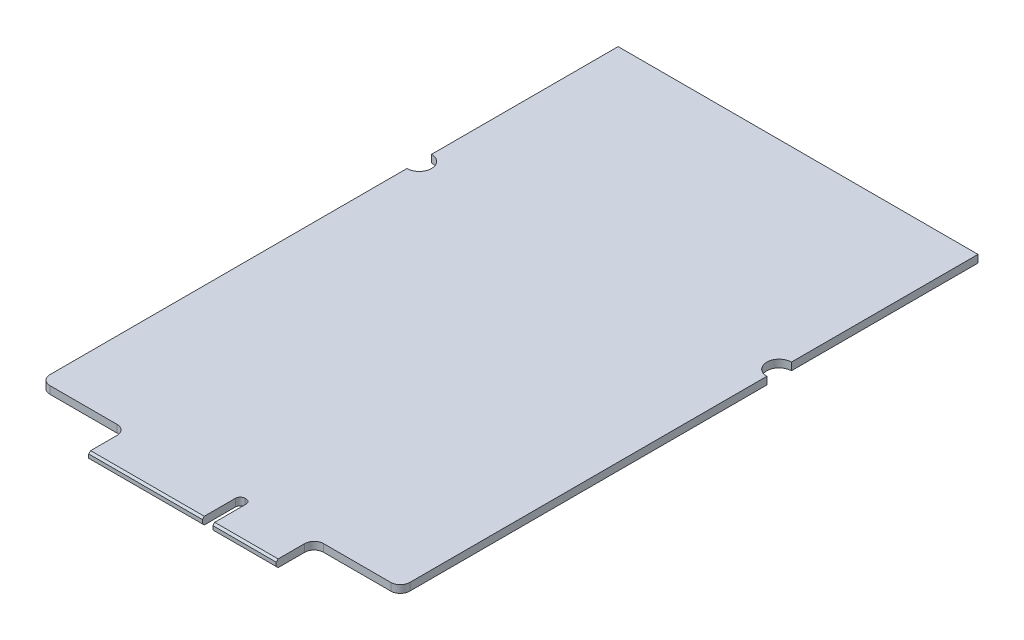
SolidWorks part; units mm, degrees
ref_plane "Front Plane" through (0, 0, 0) normal (0, 0, 1) x (1, 0, 0)
ref_plane "Top Plane" through (0, 0, 0) normal (0, 1, 0) x (1, 0, 0)
ref_plane "Right Plane" through (0, 0, 0) normal (1, 0, 0) x (0, 0, -1)
sketch "Sketch1" plane through (0, 0, 0) normal (0, 1, 0) x (1, 0, 0)
  line L0 (0, 44) -> (38, 44) construction
  line L1 (9.1, 0) -> (21.1, 0)
  line L2 (0, 4) -> (0, 42.7)
  line L3 (0, 65) -> (38, 65)
  line L4 (38, 4) -> (38, 42.7)
  line L7 (0, 4) -> (9.1, 4)
  line L8 (9.1, 0) -> (9.1, 4)
  line L11 (38, 4) -> (28.9, 4)
  line L12 (28.9, 0) -> (28.9, 4)
  line L13 (0, 45.3) -> (0, 65)
  line L14 (38, 45.3) -> (38, 65)
  line L15 (22.2, 0) -> (28.9, 0)
  line L17 (21.1, 0) -> (21.1, 4)
  line L18 (21.1, 4) -> (22.2, 4)
  line L19 (22.2, 0) -> (22.2, 4)
  arc A0 (0, 42.7) -> (0, 45.3) centre (0, 44) ccw
  arc A1 (38, 45.3) -> (38, 42.7) centre (38, 44) ccw
  point P12 (5.01, 4)
  point P20 (0, 0)
  point P21 (0, 0)
  point P22 (0, 0)
  point P23 (0, 0)
  point P24 (22.2, 11.4756)
  dimension "D5" = 2.6
  dimension "D1" = 65
  dimension "D2" = 38
  dimension "D3" = 61
  dimension "D4" = 40
  dimension "D6" = 12
  dimension "D7" = 6.7
  dimension "D8" = 1.1
extrude "Boss-Extrude1" add sketch "Sketch1" along normal blind 0.8
chamfer "Chamfer1" distance 0.2 angle 45 4 edges at (15.1, 0, 0) (25.55, 0, 0) (25.55, 0.8, 0) (15.1, 0.8, 0)
fillet "Fillet1" radius 1 4 edges at (0, 0.4, -4) (38, 0.4, -4) (9.1, 0.4, -4) (28.9, 0.4, -4)
fillet "Fillet2" radius 0.5 2 edges at (22.2, 0.4, -4) (21.1, 0.4, -4)
